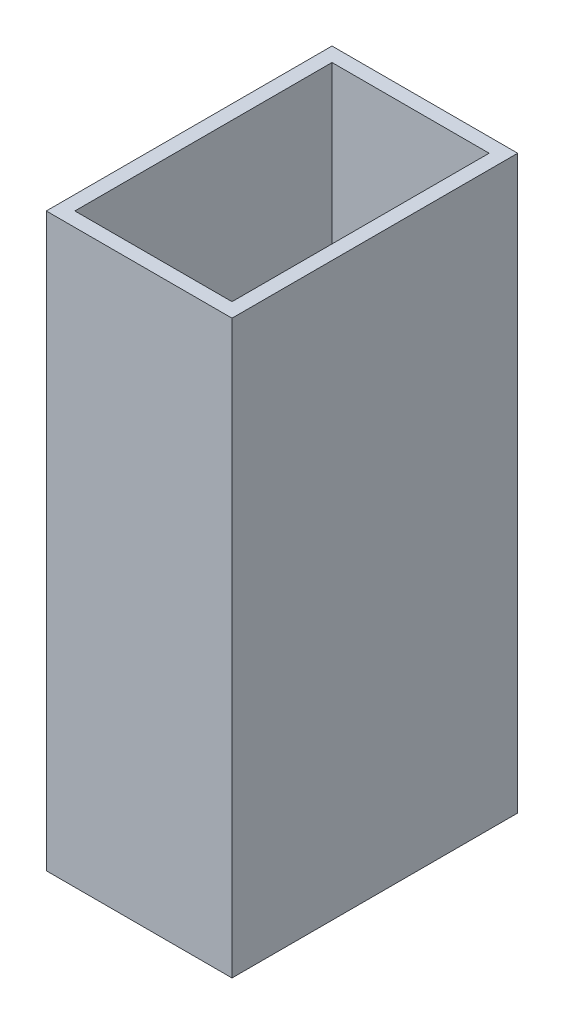
SolidWorks part; units mm, degrees
ref_plane "Front Plane" through (0, 0, 0) normal (0, 0, 1) x (1, 0, 0)
ref_plane "Top Plane" through (0, 0, 0) normal (0, 1, 0) x (1, 0, 0)
ref_plane "Right Plane" through (0, 0, 0) normal (1, 0, 0) x (0, 0, -1)
sketch "Sketch1" plane through (0, 0, 0) normal (0, 1, 0) x (1, 0, 0)
  line L0 (0, 58.5294) -> (0, -74.8529) construction
  line L1 (-32.5, 50) -> (32.5, 50)
  line L2 (-32.5, 50) -> (-32.5, -50)
  line L3 (-32.5, -50) -> (32.5, -50)
  line L4 (32.5, 50) -> (32.5, -50)
  line L5 (-67.7941, 0) -> (76.9118, 0) construction
  dimension "D1" = 100
  dimension "D2" = 65
extrude "Boss-Extrude1" add sketch "Sketch1" along normal blind 200
shell "Shell1" thickness 5
